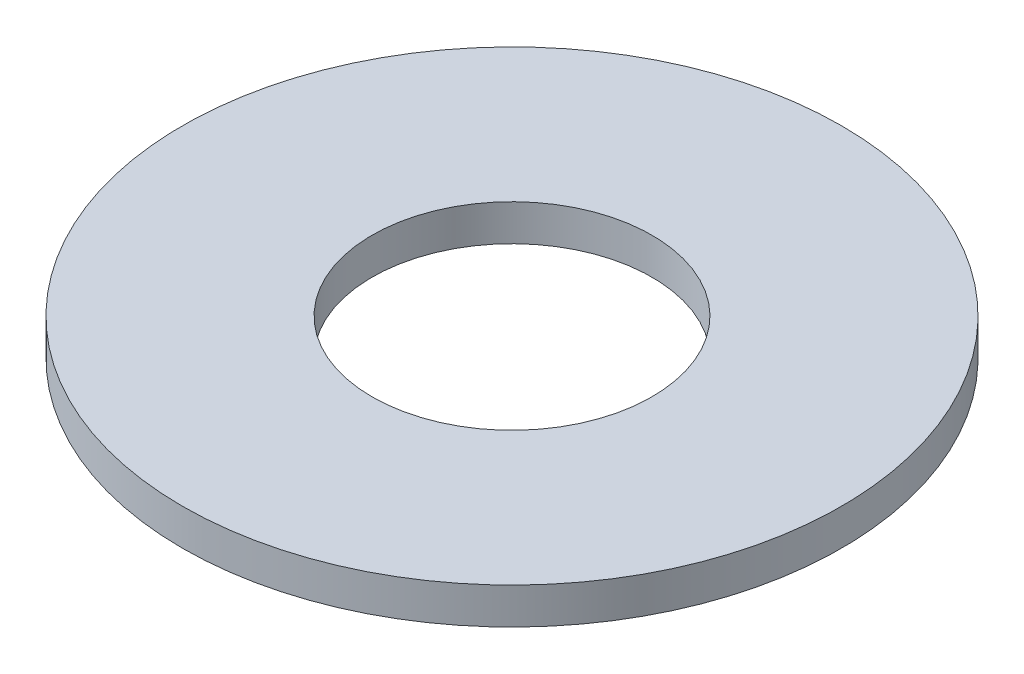
SolidWorks part; units mm, degrees
ref_plane "Front Plane" through (0, 0, 0) normal (0, 0, 1) x (1, 0, 0)
ref_plane "Top Plane" through (0, 0, 0) normal (0, 1, 0) x (1, 0, 0)
ref_plane "Right Plane" through (0, 0, 0) normal (1, 0, 0) x (0, 0, -1)
sketch "Sketch1" plane through (0, 0, 0) normal (0, 1, 0) x (1, 0, 0)
  circle A0 centre (0, 0) radius 15.875
  dimension "OD" = 31.75
extrude "Boss-Extrude1" add sketch "Sketch1" along normal blind 1.7526
sketch "Sketch5" plane through (0, 1.7526, 0) normal (0, 1, 0) x (-1, 0, 0)
  circle A0 centre (0, 0) radius 6.7437
  dimension "ID" = 13.4874
extrude "Cut-Extrude1" cut sketch "Sketch5" against normal through all
